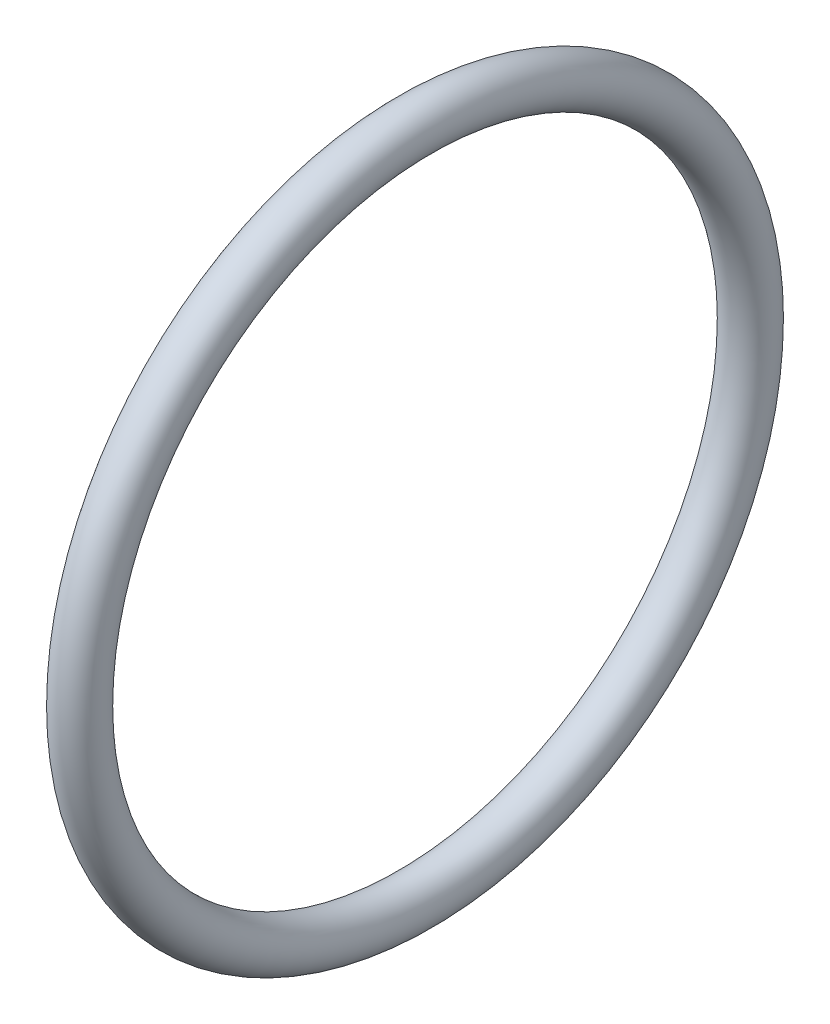
SolidWorks part; units mm, degrees
ref_plane "Front Plane" through (0, 0, 0) normal (0, 0, 1) x (1, 0, 0)
ref_plane "Top Plane" through (0, 0, 0) normal (0, 1, 0) x (1, 0, 0)
ref_plane "Right Plane" through (0, 0, 0) normal (1, 0, 0) x (0, 0, -1)
sketch "Sketch2" plane through (0, 0, 0) normal (0, 0, 1) x (1, 0, 0)
  line L0 (0, 0) -> (58.591, 0) construction
  line L2 (0, 0) -> (18.4, 0)
  line L3 (0, 0) -> (0, 2.5)
  line L4 (0, 2.5) -> (18.4, 2.5)
  line L5 (18.4, 0) -> (18.4, 2.5)
  line L6 (6.0094, 2.5) -> (6.0094, 6)
  line L11 (6.0094, 6) -> (9.9794, 6)
  line L16 (12.9794, 6) -> (12.9794, 3)
  line L17 (12.9794, 3) -> (13.6398, 3)
  line L18 (13.6398, 3) -> (13.6398, 2.5)
  line L19 (13.6398, 2.5) -> (6.0094, 2.5)
  line L22 (13.6398, 2.5) -> (16.1198, 2.5)
  line L23 (13.6398, 2.5) -> (13.6398, 4)
  line L24 (13.6398, 4) -> (16.1198, 4)
  line L25 (16.1198, 2.5) -> (16.1198, 4)
  line L27 (6.0094, 6) -> (9.9794, 6)
  line L28 (6.0094, 6) -> (6.0094, 9)
  line L29 (6.0094, 9) -> (9.9794, 9)
  line L30 (9.9794, 6) -> (9.9794, 9)
  line L31 (6.0094, 9) -> (6.0094, 8.25)
  line L32 (6.0094, 8.25) -> (5.0094, 8.25)
  line L33 (8.6609, 22.001) -> (8.6609, 12.476) construction
  line L34 (5.0094, 12.476) -> (12.3124, 12.476)
  line L35 (9.9794, 9) -> (12.3124, 9)
  line L36 (5.0094, 7.9375) -> (1.7709, 7.9375)
  line L37 (5.0094, 8.25) -> (5.0094, 12.476)
  line L38 (5.0094, 7.9375) -> (5.0094, 13.9365)
  line L39 (5.0094, 13.9365) -> (1.7709, 13.9365)
  line L40 (1.7709, 7.9375) -> (1.7709, 13.9365)
  line L41 (5.0094, 22.001) -> (12.3124, 22.001)
  line L42 (5.0094, 22.001) -> (5.0094, 30.1625)
  line L43 (5.0094, 30.1625) -> (12.3124, 30.1625)
  line L44 (12.3124, 22.001) -> (12.3124, 30.1625)
  line L49 (16.6398, 22.001) -> (16.6398, 7.5)
  line L51 (23.0198, 7.5) -> (23.0198, 6.5)
  line L54 (16.1198, 4) -> (13.6398, 4)
  line L56 (18.0398, 7.5) -> (23.0198, 7.5)
  line L57 (13.3124, 22.001) -> (16.6398, 22.001)
  line L58 (16.1198, 3.5) -> (20.0198, 3.5)
  line L59 (29.9098, 14) -> (26.9098, 11)
  line L60 (4.0094, 31.75) -> (18.0398, 31.75)
  line L61 (18.0398, 7.5) -> (23.0198, 7.5)
  line L62 (18.0398, 7.5) -> (18.0398, 12)
  line L63 (18.0398, 12) -> (23.0198, 12)
  line L64 (23.0198, 7.5) -> (23.0198, 12)
  line L65 (18.0398, 31.75) -> (18.0398, 12)
  line L66 (23.0198, 11) -> (26.9098, 11)
  line L67 (34.8098, 23) -> (31.3098, 19.5)
  line L68 (35.8098, 31) -> (38.7998, 33.99)
  line L69 (29.9098, 14) -> (29.9098, 15)
  line L70 (29.9098, 15) -> (22.9398, 15)
  line L71 (22.9398, 15) -> (21.0398, 15)
  line L72 (18.0398, 7.5) -> (16.6398, 7.5)
  line L73 (21.0398, 15) -> (21.0398, 43)
  line L74 (19.6115, 40) -> (9.6516, 40)
  line L75 (9.6516, 40) -> (4.0094, 40)
  line L76 (21.0398, 43) -> (19.6115, 43)
  line L77 (22.9398, 15) -> (29.9098, 15)
  line L78 (22.9398, 15) -> (22.9398, 21)
  line L79 (22.9398, 21) -> (29.9098, 21)
  line L80 (29.9098, 15) -> (29.9098, 21)
  line L81 (9.6516, 40) -> (19.6115, 40)
  line L82 (9.6516, 40) -> (9.6516, 50)
  line L83 (9.6516, 50) -> (19.6115, 50)
  line L84 (19.6115, 40) -> (19.6115, 50)
  line L85 (4.0094, 40) -> (4.0094, 31.75)
  line L86 (12.9794, 3) -> (12.9794, 2.5)
  line L87 (31.3098, 19.5) -> (29.9098, 19.5)
  line L88 (21.4694, 63.5) -> (21.4694, 51.308)
  line L89 (21.4694, 63.5) -> (25.9398, 63.5)
  line L90 (25.9398, 63.5) -> (25.9398, 25)
  line L91 (27.8398, 25) -> (25.9398, 25)
  line L92 (9.6516, 48) -> (8.2233, 48)
  line L93 (8.2233, 48) -> (8.2233, 53.476)
  line L94 (8.2233, 53.476) -> (19.6115, 53.476)
  line L95 (19.6115, 53.476) -> (19.6115, 50)
  line L96 (13.9174, 63.001) -> (13.9174, 53.476) construction
  line L97 (8.2233, 63.001) -> (19.6115, 63.001)
  line L98 (8.2233, 63.001) -> (8.2233, 68.2625)
  line L99 (8.2233, 68.2625) -> (19.6115, 68.2625)
  line L100 (19.6115, 63.001) -> (19.6115, 68.2625)
  line L101 (12.9794, 6) -> (11.9794, 6)
  line L102 (8.2233, 44.825) -> (4.9848, 44.825)
  line L103 (8.2233, 44.825) -> (8.2233, 54.9365)
  line L104 (8.2233, 54.9365) -> (4.9848, 54.9365)
  line L106 (9.9794, 6) -> (10.8794, 6)
  line L107 (27.8398, 25) -> (34.8098, 25)
  line L108 (34.8098, 25) -> (34.8098, 23)
  line L109 (0, 0) -> (-2, 0)
  line L110 (0, 0) -> (0, 11)
  line L111 (27.8398, 25) -> (34.8098, 25)
  line L112 (27.8398, 25) -> (27.8398, 32.5)
  line L113 (27.8398, 32.5) -> (34.8098, 32.5)
  line L114 (34.8098, 25) -> (34.8098, 32.5)
  line L115 (35.8098, 31) -> (34.8098, 31)
  line L116 (27.8398, 32.5) -> (27.8398, 64.5)
  line L117 (20.5849, 74.025) -> (6.2499, 74.025)
  line L118 (6.2499, 74.025) -> (6.2499, 76.2)
  line L119 (38.7998, 47.29) -> (30.8398, 55.25)
  line L120 (0, 11) -> (-2, 11)
  line L121 (38.7998, 43.815) -> (30.8623, 43.815)
  line L123 (-4.8152, 69.85) -> (1.5348, 76.2)
  line L124 (38.7998, 47.29) -> (38.7998, 33.99)
  line L125 (-2, 0) -> (-2, 11)
  line L126 (38.7998, 37.465) -> (30.8623, 37.465)
  line L127 (30.8623, 43.815) -> (30.8623, 37.465)
  line L128 (6.0094, 2.5) -> (6.0094, 0)
  line L129 (-0.0152, 63.5) -> (-0.0152, 30)
  line L132 (4.9848, 63.5) -> (-0.0152, 63.5)
  line L136 (-1.8152, 30) -> (-11.7752, 30)
  line L138 (-13.7752, 25.4) -> (-2, 25.4)
  line L139 (-2, 25.4) -> (-2, 11.5)
  line L140 (27.8398, 64.5) -> (20.5849, 64.5)
  line L141 (-1.8152, 30) -> (-11.7752, 30)
  line L142 (-1.8152, 30) -> (-1.8152, 39)
  line L143 (-1.8152, 39) -> (-11.7752, 39)
  line L144 (-11.7752, 30) -> (-11.7752, 39)
  line L145 (20.5849, 64.5) -> (20.5849, 74.025)
  line L146 (-12.7752, 37) -> (-12.7752, 47.29)
  line L147 (-12.7752, 37) -> (-11.7752, 37)
  line L148 (30.8398, 55.25) -> (30.8398, 76.2)
  line L149 (11.9794, 6) -> (11.9794, 5.45)
  line L154 (-2, 11.5) -> (0.5, 11.5)
  line L155 (4.9848, 60.6197) -> (24.0348, 60.6197)
  line L160 (4.9848, 60.6197) -> (4.9848, 55.8572)
  line L161 (4.9848, 55.8572) -> (24.0348, 55.8572)
  line L166 (24.0348, 60.6197) -> (24.0348, 55.8572)
  line L167 (4.9848, 60.6197) -> (24.0348, 55.8572) construction
  line L172 (4.9848, 55.8572) -> (24.0348, 60.6197) construction
  line L173 (24.0348, 62.2072) -> (25.9398, 62.2072)
  line L174 (11.9794, 5.45) -> (10.8794, 5.45)
  line L175 (10.8794, 6) -> (10.8794, 5.45)
  line L176 (24.0348, 62.2072) -> (24.0348, 54.2697)
  line L177 (24.0348, 54.2697) -> (25.9398, 54.2697)
  line L178 (25.9398, 62.2072) -> (25.9398, 54.2697)
  line L179 (24.0348, 62.2072) -> (25.9398, 54.2697) construction
  line L180 (24.0348, 54.2697) -> (25.9398, 62.2072) construction
  line L181 (3, 19.6197) -> (15.7, 19.6197)
  line L182 (3, 19.6197) -> (3, 14.8572)
  line L183 (3, 14.8572) -> (15.7, 14.8572)
  line L184 (15.7, 19.6197) -> (15.7, 14.8572)
  line L185 (3, 19.6197) -> (15.7, 14.8572) construction
  line L186 (3, 14.8572) -> (15.7, 19.6197) construction
  line L187 (15.7, 21.2072) -> (16.6398, 21.2072)
  line L188 (15.7, 21.2072) -> (15.7, 13.2697)
  line L189 (15.7, 13.2697) -> (16.6398, 13.2697)
  line L190 (16.6398, 21.2072) -> (16.6398, 13.2697)
  line L191 (15.7, 21.2072) -> (16.6398, 13.2697) construction
  line L192 (15.7, 13.2697) -> (16.6398, 21.2072) construction
  line L193 (0.5, 11.5) -> (0.5, 6.9375)
  line L194 (0.5, 6.9375) -> (1.7709, 6.9375)
  line L195 (23.0198, 6.5) -> (20.0198, 3.5)
  line L196 (4.9848, 63.5) -> (4.9848, 54.9365)
  line L197 (3, 43.825) -> (4.9848, 43.825)
  line L198 (1.7709, 6.9375) -> (1.7709, 7.9375)
  line L199 (6.0094, 0) -> (12.9794, 0)
  line L200 (12.9794, 0) -> (12.9794, 2.5)
  line L201 (18.0398, 31.75) -> (18.0398, 35.875)
  line L202 (18.0398, 35.875) -> (21.0398, 35.875)
  line L203 (30.8398, 76.2) -> (6.2499, 76.2)
  line L204 (2.8049, 69.85) -> (7.2499, 69.85) construction
  line L205 (7.2499, 67.4688) -> (26.2999, 67.4688)
  line L206 (7.2499, 74.025) -> (7.2499, 64.5)
  line L207 (7.2499, 64.5) -> (-1.8152, 64.5)
  line L208 (-1.8152, 64.5) -> (-1.8152, 39)
  line L209 (-12.7752, 47.29) -> (-4.8152, 55.25)
  line L210 (-4.8152, 55.25) -> (-4.8152, 69.85)
  line L211 (7.2499, 67.4688) -> (7.2499, 72.2312)
  line L212 (7.2499, 72.2312) -> (26.2999, 72.2313)
  line L213 (26.2999, 67.4688) -> (26.2999, 72.2313)
  line L214 (26.2999, 73.8187) -> (30.8398, 73.8187)
  line L215 (26.2999, 73.8187) -> (26.2999, 65.8813)
  line L216 (26.2999, 65.8813) -> (30.8398, 65.8813)
  line L217 (30.8398, 73.8187) -> (30.8398, 65.8813)
  line L218 (2.8049, 72.2313) -> (25.0299, 72.2313)
  line L219 (2.8049, 72.2313) -> (2.8049, 67.4687)
  line L220 (2.8049, 67.4687) -> (25.0299, 67.4687)
  line L221 (25.0299, 72.2313) -> (25.0299, 67.4687)
  line L222 (25.0299, 69.85) -> (20.5849, 69.85) construction
  line L223 (21.4694, 51.308) -> (22.9398, 51.308)
  line L224 (22.9398, 51.308) -> (22.9398, 21)
  line L225 (13.6398, 4) -> (13.6398, 12.2697)
  line L226 (13.6398, 12.2697) -> (13.3124, 12.2697)
  line L227 (13.3124, 12.2697) -> (13.3124, 22.001)
  line L228 (12.3124, 9) -> (12.3124, 12.476)
  line L229 (-1.8152, 30) -> (-0.0152, 30)
  line L230 (8.2233, 65.6317) -> (2.8049, 65.6317) construction
  line L231 (19.6115, 65.6317) -> (25.0299, 65.6317) construction
  line L232 (1.5348, 76.2) -> (6.2499, 76.2)
  line L233 (-11.7752, 30) -> (-13.7752, 30)
  line L234 (-13.7752, 30) -> (-13.7752, 25.4)
  line L235 (3, 13.9365) -> (3, 43.825)
  line L236 (4.9848, 54.9365) -> (4.9848, 44.825)
  line L237 (4.9848, 43.825) -> (4.9848, 44.825)
  circle A0 centre (26.8898, 25.95) radius 0.95
  circle A1 centre (21.9898, 15.95) radius 0.95
  circle A2 centre (17.3398, 8.2) radius 0.7
  circle A3 centre (10.4294, 6.45) radius 0.45
  circle A4 centre (-0.9152, 30.9) radius 0.9
  point P7 (24.9873, 58.2385)
  point P131 (16.1699, 17.2385)
  point P135 (14.5098, 58.2385)
  point P146 (9.35, 17.2385)
sketch "Sketch3" plane through (0, 0, 0) normal (0, 0, 1) x (1, 0, 0)
  circle A0 centre (10.4294, 6.45) radius 0.45 construction
  circle A1 centre (10.4294, 6.45) radius 0.45
revolve "Revolve1" add sketch "Sketch3" angle 360 about L0
